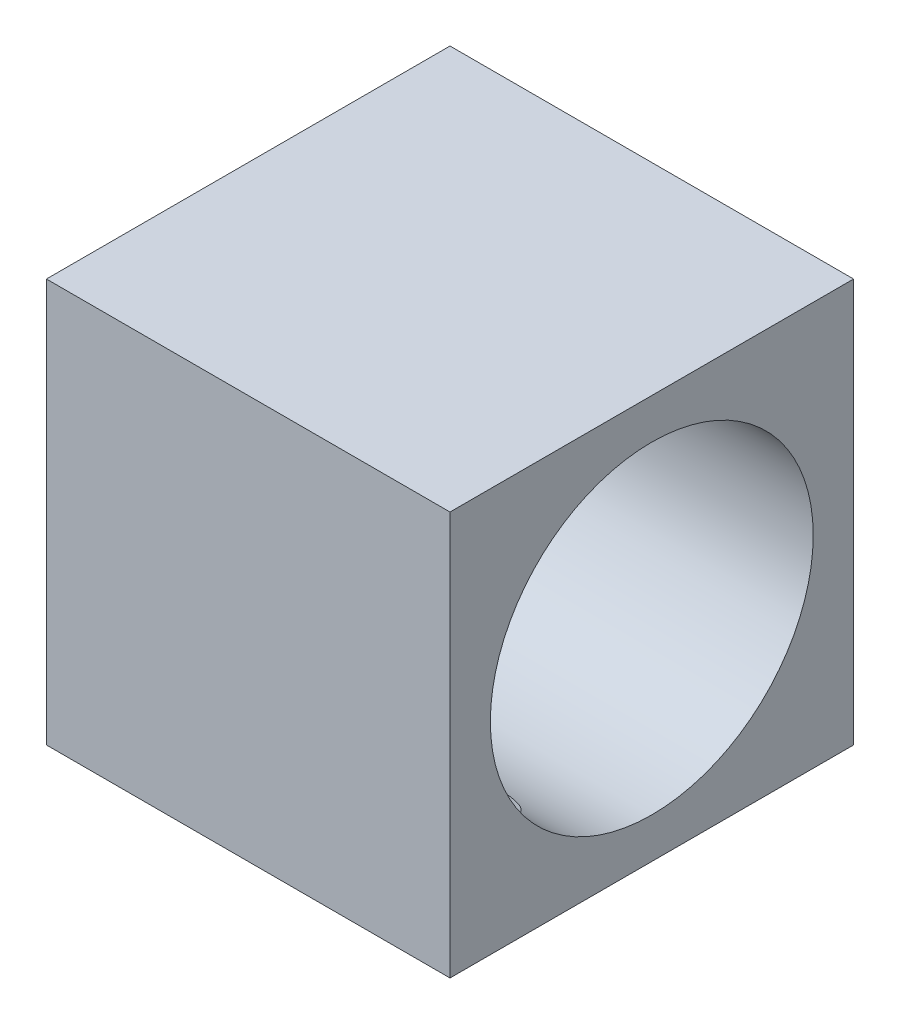
SolidWorks part; units mm, degrees
ref_plane "Front Plane" through (0, 0, 0) normal (0, 0, 1) x (1, 0, 0)
ref_plane "Top Plane" through (0, 0, 0) normal (0, 1, 0) x (1, 0, 0)
ref_plane "Right Plane" through (0, 0, 0) normal (1, 0, 0) x (0, 0, -1)
sketch "Sketch1" plane through (0, 0, 0) normal (0, 1, 0) x (1, 0, 0)
  line L1 (-10, -10) -> (10, -10)
  line L2 (-10, -10) -> (-10, 10)
  line L3 (-10, 10) -> (10, 10)
  line L4 (10, -10) -> (10, 10)
  line L5 (-10, -10) -> (10, 10) construction
  line L6 (-10, 10) -> (10, -10) construction
  point P0 (0, 0)
  dimension "D1" = 20
  dimension "D2" = 20
extrude "Boss-Extrude1" add sketch "Sketch1" along normal blind 20
sketch "Sketch2" plane through (0, 0, 0) normal (1, 0, 0) x (0, 0, -1)
  circle A0 centre (0, 10) radius 8
  dimension "D2" = 16
  dimension "D1" = 10
extrude "Cut-Extrude1" cut sketch "Sketch2" against normal blind 20 and the other way blind 20
sketch "Sketch3" plane through (0, 0, 0) normal (0, -1, 0) x (-1, 0, 0)
  circle A0 centre (-6, -6) radius 2.5
  circle A1 centre (6, 6) radius 2.5
  dimension "D1" = 5
  dimension "D2" = 5
  dimension "D5" = 6
  dimension "D3" = 6
  dimension "D4" = 6
  dimension "D6" = 6
extrude "Cut-Extrude2" cut sketch "Sketch3" against normal blind 5
